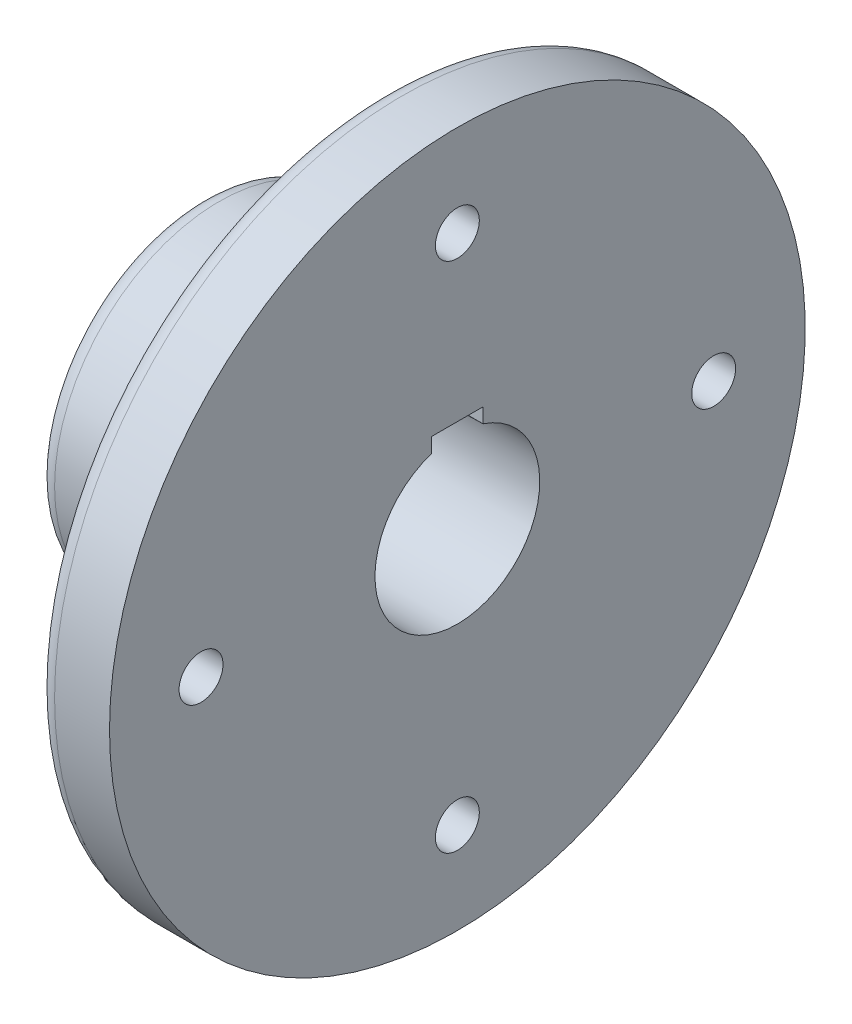
SolidWorks part; units mm, degrees
ref_plane "Front Plane" through (0, 0, 0) normal (0, 0, 1) x (1, 0, 0)
ref_plane "Top Plane" through (0, 0, 0) normal (0, 1, 0) x (1, 0, 0)
ref_plane "Right Plane" through (0, 0, 0) normal (1, 0, 0) x (0, 0, -1)
sketch "Sketch2" plane through (0, 0, 0) normal (0, 1, 0) x (1, 0, 0)
  line L0 (0, 5) -> (0, 45)
  line L2 (5, 0) -> (45, 0)
  line L3 (50, -5) -> (50, -45)
  line L7 (70, -50) -> (55, -50)
  line L8 (0, 45) -> (70, 45) construction
  line L9 (70, -50) -> (70, 22.5)
  line L10 (70, 45) -> (70, 22.5)
  line L11 (70, 22.5) -> (0, 22.5)
  arc A0 (50, -45) -> (55, -50) centre (55, -45) ccw
  arc A1 (45, 0) -> (50, -5) centre (45, -5) cw
  arc A2 (0, 5) -> (5, 0) centre (5, 5) ccw
  point P11 (50, -50)
  point P14 (50, 0)
  point P17 (0, 0)
  point P20 (0, 90)
  point P23 (50, 90)
  point P26 (50, 140)
  dimension "D6" = 5
  dimension "D1" = 22.5
revolve "Revolve1" add sketch "Sketch2" angle 360 about L8
sketch "Sketch10" plane through (70, 0, 0) normal (1, 0, 0) x (0, 0, -1)
  circle A1 centre (45, -70) radius 6
  circle A2 centre (-25, 0) radius 6
  circle A3 centre (45, 70) radius 6
  circle A4 centre (115, 0) radius 6
  point P14 (45, 0)
  dimension "D1" = 4
extrude "Cut-Extrude2" cut sketch "Sketch10" against normal through all
sketch "Sketch11" plane through (70, 0, 0) normal (1, 0, 0) x (0, 0, -1)
  line L0 (38, 25.4) -> (38, 21.3834)
  line L2 (45, 25.4) -> (38, 25.4)
  line L3 (45, 25.4) -> (52, 25.4)
  line L4 (52, 25.4) -> (52, 21.3834)
  line L5 (38, 21.3834) -> (38, 21.2845)
  line L6 (38, 21.2845) -> (52, 21.3834)
  circle A0 centre (45, 0) radius 22.5 construction
  dimension "D1" = 7
  dimension "D3" = 7
extrude "Cut-Extrude4" cut sketch "Sketch11" against normal through all draft 0.57
